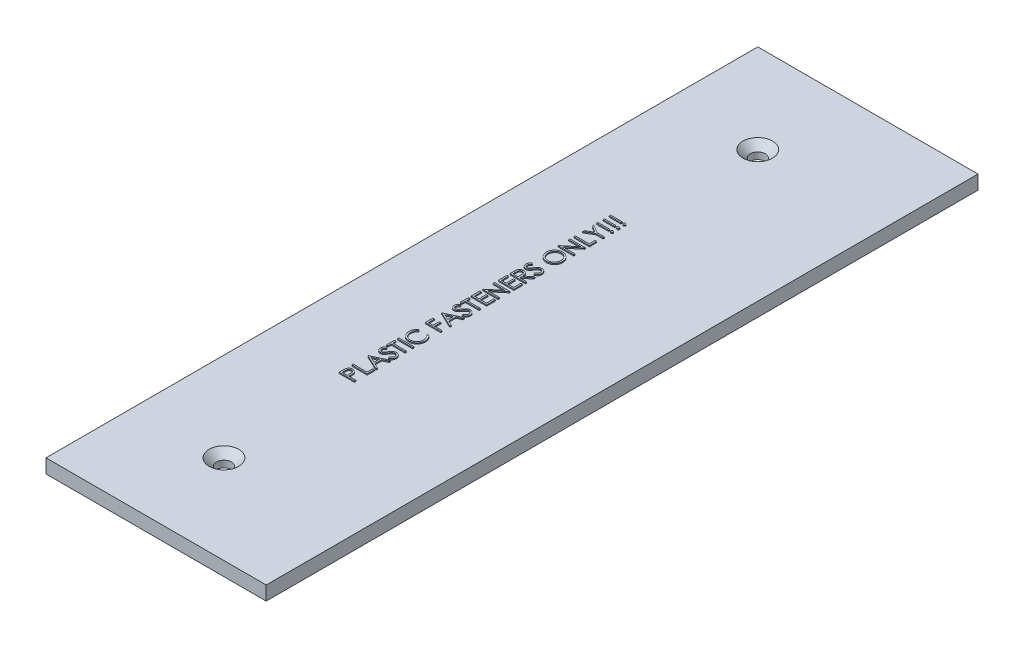
SolidWorks part; units mm, degrees
material "ABS"
ref_plane "Front Plane" through (0, 0, 0) normal (0, 0, 1) x (1, 0, 0)
ref_plane "Top Plane" through (0, 0, 0) normal (0, 1, 0) x (1, 0, 0)
ref_plane "Right Plane" through (0, 0, 0) normal (1, 0, 0) x (0, 0, -1)
sketch "Sketch1" plane through (0, 0, 0) normal (0, 1, 0) x (1, 0, 0)
  line L1 (0, 0) -> (50, 0)
  line L2 (0, 0) -> (0, 161.6)
  line L3 (0, 161.6) -> (50, 161.6)
  line L4 (50, 0) -> (50, 161.6)
  dimension "D1" = 50
  dimension "D2" = 161.6
extrude "Boss-Extrude1" add sketch "Sketch1" along normal blind 3.175
hole_wizard "CSK for M3 SFHCS1" positions "Sketch3" profile "Sketch2" countersink size "M3" standard "ANSI Metric" end condition through all
sketch "Sketch3" plane through (0, 3.175, 0) normal (0, 1, 0) x (1, 0, 0)
  line L0 (20.2, 0) -> (20.2, 161.6) construction
  line L1 (0, 0) -> (50, 0) construction
  line L2 (50, 161.6) -> (0, 161.6) construction
  line L4 (0, 161.6) -> (0, 0) construction
  point P10 (20.2, 20.2)
  point P12 (20.2, 141.4)
  dimension "D1" = 20.2
  dimension "D2" = 20.2
  dimension "D3" = 20.2
sketch "Sketch2" plane through (20.2, 3.175, -20.2) normal (1, 0, 0) x (0, 0, 1)
  line L0 (0, 0) -> (0, 3.175)
  line L1 (0, 3.175) -> (1.7, 3.175)
  line L2 (1.7, 3.175) -> (1.7, 1.66)
  line L3 (1.7, 1.66) -> (3.36, 0)
  line L5 (3.36, 0) -> (0, 0)
  line L6 (-1.7, 1.66) -> (-3.36, 0) construction
  line L11 (0, -6.35) -> (0, 107.95) construction
  dimension "Thru Hole Dia." = 3.4
  dimension "Thru Hole Depth" = 3.175
  dimension "Near C'Sink Dia." = 6.72
  dimension "Near C'Sink Angle" = 90
sketch "Sketch4" plane through (0, 3.175, 0) normal (0, 1, 0) x (1, 0, 0)
  line L0 (20.2, 20.2) -> (20.2, 141.4) construction
  text T0 "PLASTIC FASTENERS ONLY!!!"
extrude "Boss-Extrude2" add sketch "Sketch4" along normal blind 0.25
equation "\"ABS_thickness\" = 1.59\t"
equation "\"ABS_thickness_1/8\" = 3.175\t"
equation "\"Bus_bar_thickness\" = 3.175"
equation "\"Connector_width\" = 20.2"
equation "\"Number_of_cells_long\" = 25"
equation "\"Number_of_cells_wide\" = 2"
equation "\"Cell_height\" = 65.0"
equation "\"Cell_diam\" = 18.0"
equation "\"D1@Boss-Extrude1\"=\"ABS_thickness_1/8\""
equation "\"D2@Sketch1\"=\"Connector_width\"*8"
equation "\"D1@Sketch3\"=\"Connector_width\""
equation "\"D2@Sketch3\"=\"Connector_width\""
equation "\"D3@Sketch3\"=\"Connector_width\""
